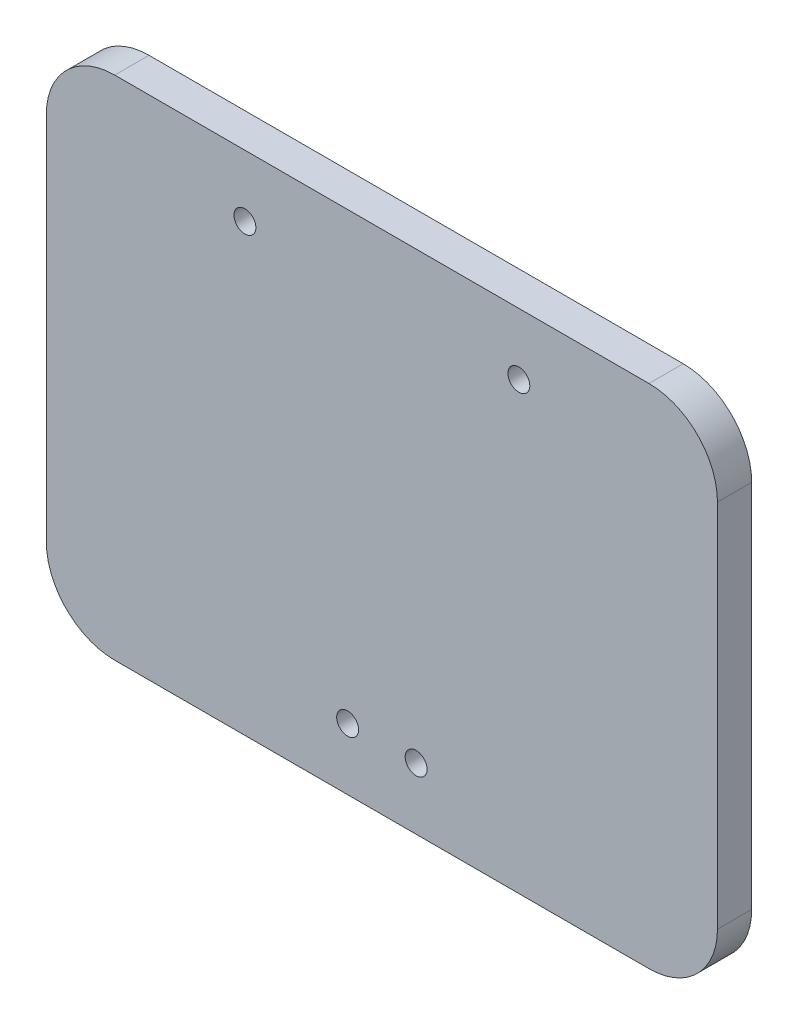
SolidWorks part; units mm, degrees
ref_plane "Спереди" through (0, 0, 0) normal (0, 0, 1) x (1, 0, 0)
ref_plane "Сверху" through (0, 0, 0) normal (0, 1, 0) x (1, 0, 0)
ref_plane "Справа" through (0, 0, 0) normal (1, 0, 0) x (0, 0, -1)
sketch "Эскиз2" plane through (0, 0, 0) normal (0, 0, 1) x (1, 0, 0)
  line L1 (-39, 37) -> (39, 37)
  line L2 (-49, 27) -> (-49, -27)
  line L3 (-39, -37) -> (39, -37)
  line L4 (49, 27) -> (49, -27)
  line L5 (-49, 37) -> (49, -37) construction
  line L6 (-49, -37) -> (49, 37) construction
  arc A0 (-49, -27) -> (-39, -37) centre (-39, -27) ccw
  arc A1 (39, -37) -> (49, -27) centre (39, -27) ccw
  arc A2 (39, 37) -> (49, 27) centre (39, 27) cw
  arc A3 (-39, 37) -> (-49, 27) centre (-39, 27) ccw
  point P0 (0, 0)
  dimension "D3" = 10
  dimension "D1" = 98
  dimension "D2" = 74
extrude "Бобышка-Вытянуть1" add sketch "Эскиз2" along normal blind 5
sketch "Эскиз3" plane through (0, 0, 5) normal (0, 0, 1) x (1, 0, 0)
  line L0 (0, -37) -> (0, 37) construction
  line L1 (-39, -37) -> (39, -37) construction
  line L2 (39, 37) -> (-39, 37) construction
  circle A0 centre (5, -28) radius 1.6
  circle A1 centre (-5, -28) radius 1.6
  circle A2 centre (-20, 28) radius 1.6
  circle A3 centre (20, 28) radius 1.6
  dimension "D1" = 3.2
  dimension "D2" = 10
  dimension "D5" = 9
  dimension "D3" = 40
  dimension "D4" = 9
extrude "Вырез-Вытянуть1" cut sketch "Эскиз3" against normal blind 5
